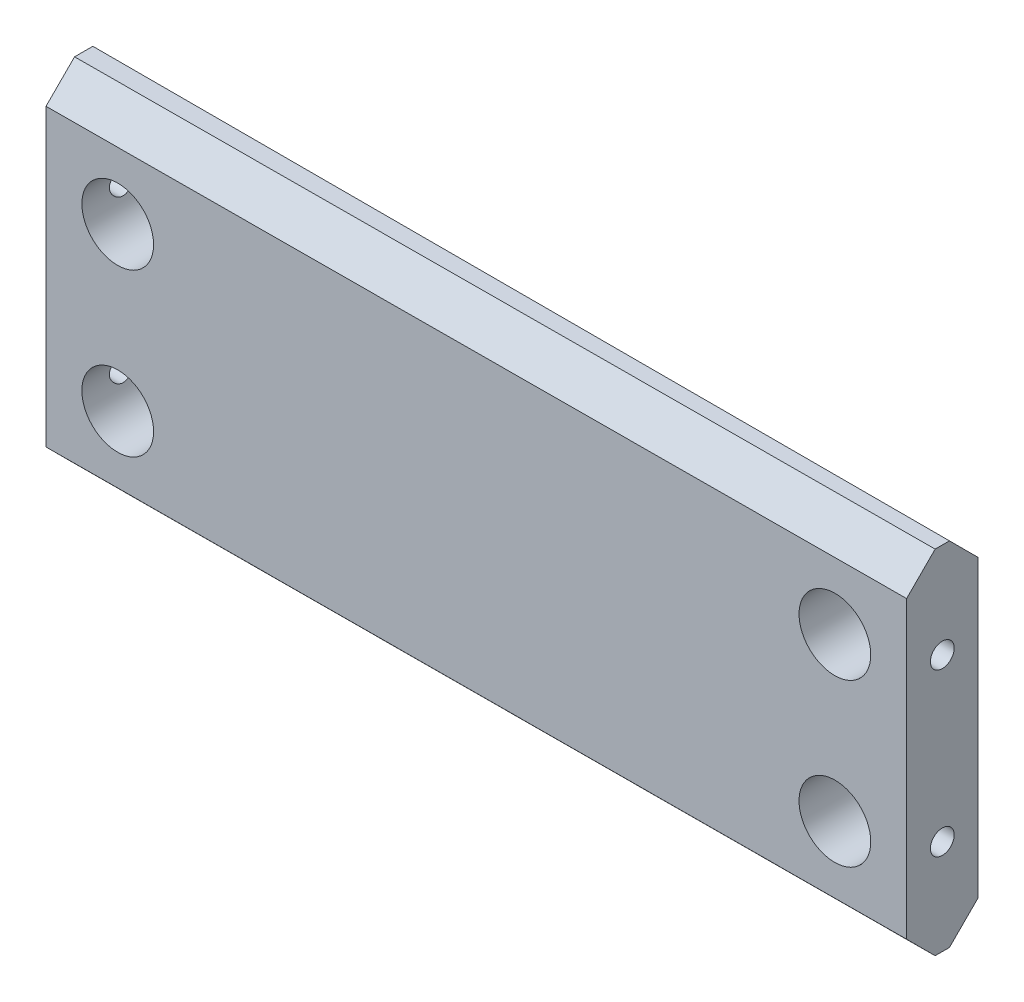
SolidWorks part; units mm, degrees
material "Pine"
ref_plane "Front Plane" through (0, 0, 0) normal (0, 0, 1) x (1, 0, 0)
ref_plane "Top Plane" through (0, 0, 0) normal (0, 1, 0) x (1, 0, 0)
ref_plane "Right Plane" through (0, 0, 0) normal (1, 0, 0) x (0, 0, -1)
sketch3d "3DSketch2"
  line L0 (-117.4118, 0, -9.7844) -> (111.1882, 0, -9.7844)
  line L1 (-117.4118, 0, -9.7844) -> (-117.4118, 0, 10.3321)
  line L3 (111.1882, 0, -9.7844) -> (111.1857, 0, 9.2656)
  line L4 (-117.4118, 0, 10.3321) -> (111.1857, 0, 9.2656)
  line L5 (-117.4118, 0, -9.7844) -> (111.1857, 0, 9.2656) construction
  line L6 (111.1882, 0, -9.7844) -> (-117.4118, 0, 10.3321) construction
  point P0 (0, 0, 0)
  dimension "D1" = 228.6
  dimension "D2" = 19.05
  dimension "D3" = 228.6
  dimension "D4" = 90
extrude "Boss-Extrude3" add sketch "3DSketch2" along direction (0, 1, 0) on the side of the normal mid plane 93.98
chamfer "Chamfer1" distance 7.62 angle 45 4 edges
hole_wizard "3/4 (0.75) Diameter Hole1" positions "Sketch4" profile "Sketch3" hole size "3/4" standard "Ansi Inch"
sketch "Sketch4" plane through (0.0456, 0, 9.7841) normal (0.0047, 0, 1) x (1, 0, -0.0047)
  line L0 (111.1413, -39.37) -> (111.1413, 39.37) construction
  line L1 (111.1779, -46.99) -> (-117.4231, -46.99) construction
  line L2 (-117.4587, -39.37) -> (-117.4587, 39.37) construction
  point P0 (92.0913, -21.59)
  point P6 (-98.4087, -21.59)
  dimension "D1" = 19.05
  dimension "D2" = 25.4
  dimension "D3" = 19.05
  dimension "D4" = 25.4
sketch "Sketch3" plane through (92.1359, -21.59, 9.3545) normal (0, 1, 0) x (1, 0, -0.0047)
  line L0 (0, 0) -> (0, 24.7732)
  line L1 (0, 24.7732) -> (9.525, 19.05)
  line L2 (9.525, 19.05) -> (9.525, 0)
  line L5 (9.525, 0) -> (0, 0)
  line L10 (0, 24.7732) -> (-9.525, 19.05) construction
  line L11 (0, -6.35) -> (0, 107.95) construction
  dimension "Hole Dia." = 19.05
  dimension "Hole Depth" = 19.05
  dimension "Drill Angle" = 118
hole_wizard "1/4 (0.25) Diameter Hole1" positions "Sketch6" profile "Sketch5" hole size "1/4" standard "Ansi Inch"
sketch "Sketch6" plane through (111.187, 0, 0.0145) normal (1, 0, 0.0001) x (0.0001, 0, -1)
  line L0 (-1.631, -46.99) -> (2.1789, -46.99) construction
  line L1 (-9.2511, -39.37) -> (-9.2511, 39.37) construction
  point P0 (0.2739, -21.59)
  dimension "D1" = 25.4
  dimension "D2" = 9.525
sketch "Sketch5" plane through (111.187, -21.59, -0.2594) normal (0, 1, 0) x (0.0001, 0, -1)
  line L0 (0, 0) -> (0, 20.9577)
  line L1 (0, 20.9577) -> (3.175, 19.05)
  line L2 (3.175, 19.05) -> (3.175, 0)
  line L5 (3.175, 0) -> (0, 0)
  line L10 (0, 20.9577) -> (-3.175, 19.05) construction
  line L11 (0, -6.35) -> (0, 107.95) construction
  dimension "Hole Dia." = 6.35
  dimension "Hole Depth" = 19.05
  dimension "Drill Angle" = 118
hole_wizard "1/4 (0.25) Diameter Hole2" positions "Sketch8" profile "Sketch7" hole size "1/4" standard "Ansi Inch"
sketch "Sketch8" plane through (-117.4118, 0, 0) normal (-1, 0, 0) x (0, 0, 1)
  line L0 (-2.1644, -46.99) -> (2.712, -46.99) construction
  line L1 (-9.7844, -39.37) -> (-9.7844, 39.37) construction
  point P0 (-0.2594, -21.59)
  dimension "D1" = 25.4
  dimension "D2" = 9.525
sketch "Sketch7" plane through (-117.4118, -21.59, -0.2594) normal (0, 1, 0) x (0, 0, 1)
  line L0 (0, 0) -> (0, 20.9577)
  line L1 (0, 20.9577) -> (3.175, 19.05)
  line L2 (3.175, 19.05) -> (3.175, 0)
  line L5 (3.175, 0) -> (0, 0)
  line L10 (0, 20.9577) -> (-3.175, 19.05) construction
  line L11 (0, -6.35) -> (0, 107.95) construction
  dimension "Hole Dia." = 6.35
  dimension "Hole Depth" = 19.05
  dimension "Drill Angle" = 118
mirror "Mirror9" about plane through (0, 0, 0) normal (0, 1, 0) of "1/4 (0.25) Diameter Hole1", "1/4 (0.25) Diameter Hole2", "3/4 (0.75) Diameter Hole1"
